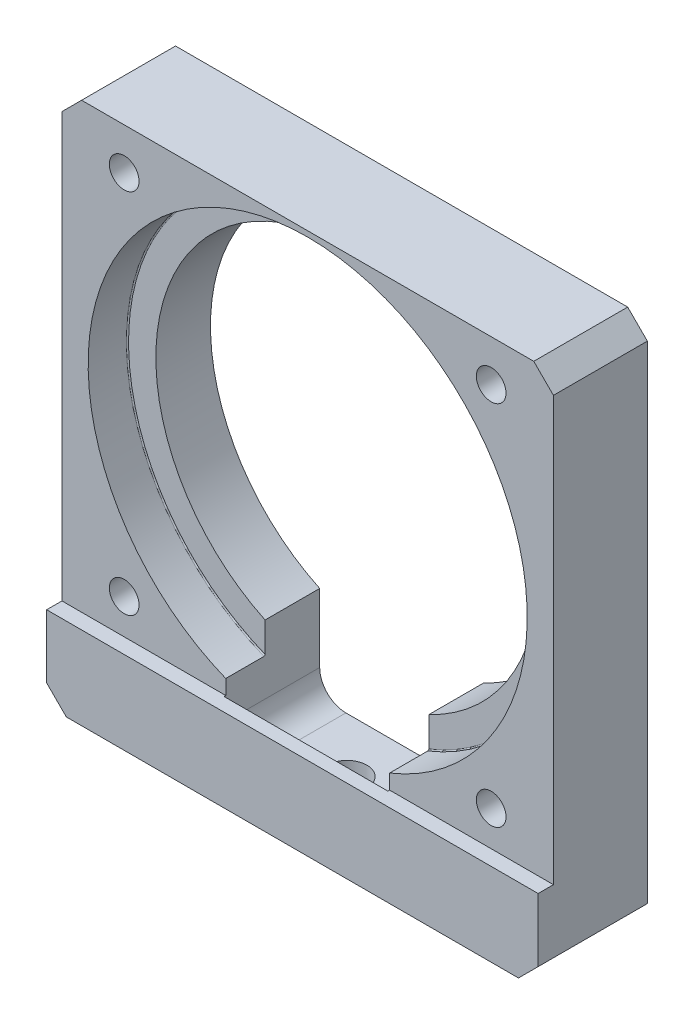
SolidWorks part; units mm, degrees
material "304 SSTL"
ref_plane "Front" through (0, 0, 0) normal (0, 0, 1) x (1, 0, 0)
ref_plane "Top" through (0, 0, 0) normal (0, 1, 0) x (1, 0, 0)
ref_plane "Right" through (0, 0, 0) normal (1, 0, 0) x (0, 0, -1)
sketch "Sketch1" plane through (0, 0, 0) normal (0, 0, 1) x (1, 0, 0)
  line L1 (0, 0) -> (57.15, 0)
  line L2 (0, 0) -> (0, 61.214)
  line L3 (0, 61.214) -> (57.15, 61.214)
  line L4 (57.15, 0) -> (57.15, 61.214)
  dimension "D1" = 57.15
  dimension "D2" = 61.214
extrude "Boss-Extrude1" add sketch "Sketch1" along normal mid plane 12.7
sketch "Sketch2" plane through (0, 0, 6.35) normal (0, 0, 1) x (1, 0, 0)
  line L0 (0, 61.214) -> (0, 0) construction
  line L1 (0, 61.214) -> (57.15, 61.214)
  line L2 (0, 61.214) -> (0, 9.652)
  line L3 (0, 9.652) -> (57.15, 9.652)
  line L4 (57.15, 61.214) -> (57.15, 9.652)
  line L5 (57.15, 0) -> (57.15, 61.214) construction
  line L6 (57.15, 61.214) -> (0, 61.214) construction
  dimension "D1" = 51.562
extrude "Cut-Extrude1" cut sketch "Sketch2" against normal blind 1.778
hole_wizard "1 (1) Diameter Hole1" positions "Sketch4" profile "Sketch5" hole size "1" standard "Ansi Inch" end condition through all
sketch "Sketch4" plane through (0, 0, 4.572) normal (0, 0, 1) x (1, 0, 0)
  line L0 (28.575, 35.052) -> (28.575, 61.214) construction
  line L1 (57.15, 61.214) -> (0, 61.214) construction
  line L2 (0, 9.652) -> (57.15, 9.652) construction
  point P0 (28.575, 35.052)
  dimension "D1" = 25.4
sketch "Sketch5" plane through (28.575, 35.052, 4.572) normal (1, 0, 0) x (0, -1, 0)
  line L0 (0, 0) -> (0, 10.922)
  line L1 (0, 10.922) -> (22.225, 10.922)
  line L2 (22.225, 10.922) -> (22.225, 0)
  line L5 (22.225, 0) -> (0, 0)
  line L11 (0, -6.35) -> (0, 107.95) construction
  dimension "Thru Hole Dia." = 44.45
  dimension "Thru Hole Depth" = 10.922
sketch "Sketch6" plane through (0, 0, -6.35) normal (0, 0, -1) x (-1, 0, 0)
  line L1 (-35.052, 3.9624) -> (-22.098, 3.9624)
  line L2 (-38.1, 7.0104) -> (-38.1, 20.9536)
  line L3 (-38.1, 20.9536) -> (-19.05, 20.9536)
  line L4 (-19.05, 7.0104) -> (-19.05, 20.9536)
  line L5 (-28.575, 3.9624) -> (-28.575, 20.9536) construction
  line L6 (-28.575, 20.9536) -> (-28.575, 61.214) construction
  line L7 (-57.15, 61.214) -> (0, 61.214) construction
  line L8 (0, 0) -> (-57.15, 0) construction
  arc A0 (-22.098, 3.9624) -> (-19.05, 7.0104) centre (-22.098, 7.0104) ccw
  arc A1 (-38.1, 7.0104) -> (-35.052, 3.9624) centre (-35.052, 7.0104) ccw
  point P13 (-19.05, 3.9624)
  point P16 (-38.1, 3.9624)
  dimension "D3" = 3.048
  dimension "D1" = 19.05
  dimension "D2" = 3.9624
extrude "Cut-Extrude2" cut sketch "Sketch6" against normal blind 11.1252
hole_wizard "#14 (0.182) Diameter Hole1" positions "Sketch9" profile "Sketch8" hole size "#14" standard "Ansi Inch"
sketch "Sketch9" plane through (0, 3.9624, 0) normal (0, 1, 0) x (-1, 0, 0)
  line L0 (0, 0) -> (-28.575, 0) construction
  line L1 (-28.575, 0) -> (-28.575, -6.35) construction
  line L2 (0, -6.35) -> (-57.15, -6.35) construction
  point P0 (-28.575, 0)
sketch "Sketch8" plane through (28.575, 3.9624, 0) normal (1, 0, 0) x (0, 0, 1)
  line L0 (0, 0) -> (0, 15.3588)
  line L1 (0, 15.3588) -> (2.3114, 13.97)
  line L2 (2.3114, 13.97) -> (2.3114, 0)
  line L5 (2.3114, 0) -> (0, 0)
  line L10 (0, 15.3588) -> (-2.3114, 13.97) construction
  line L11 (0, -6.35) -> (0, 107.95) construction
  dimension "Hole Dia." = 4.6228
  dimension "Hole Depth" = 13.97
  dimension "Drill Angle" = 118
sketch "Sketch10" plane through (0, 0, 4.572) normal (0, 0, 1) x (1, 0, 0)
  circle A0 centre (28.575, 35.052) radius 25.527
  dimension "D1" = 51.054
extrude "Cut-Extrude3" cut sketch "Sketch10" against normal blind 4.572
chamfer "Chamfer1" distance 2.286 angle 45 4 edges at (57.15, 61.214, -0.889) (57.15, 0, 0) (0, 0, 0) (0, 61.214, -0.889)
hole_wizard "#8-32 Tapped Hole1" positions "Sketch12" profile "Sketch11" tap size "#8-32" standard "Ansi Inch" end condition through all
sketch "Sketch12" plane through (0, 0, 4.572) normal (0, 0, 1) x (1, 0, 0)
  line L0 (7.239, 56.388) -> (49.911, 56.388) construction
  line L1 (7.239, 56.388) -> (7.239, 13.716) construction
  line L2 (7.239, 13.716) -> (49.911, 13.716) construction
  line L3 (49.911, 56.388) -> (49.911, 13.716) construction
  line L4 (28.575, 35.052) -> (28.575, 56.388) construction
  line L5 (28.575, 35.052) -> (49.911, 35.052) construction
  point P0 (7.239, 56.388)
  point P1 (49.911, 56.388)
  point P3 (7.239, 13.716)
  point P5 (49.911, 13.716)
  dimension "D1" = 42.672
sketch "Sketch11" plane through (7.239, 56.388, 4.572) normal (1, 0, 0) x (0, -1, 0)
  line L0 (0, 0) -> (0, 10.922)
  line L1 (0, 10.922) -> (1.7272, 10.922)
  line L2 (1.7272, 10.922) -> (1.7272, 0)
  line L5 (1.7272, 0) -> (0, 0)
  line L11 (0, -6.35) -> (0, 107.95) construction
  dimension "Thru Tap Drill Dia." = 3.4544
  dimension "Thru Tap Drill Depth" = 10.922
cosmetic thread "Hole Thread1" parameters "D2"=4.1656
cosmetic thread "Hole Thread2" parameters "D2"=4.1656
cosmetic thread "Hole Thread3" parameters "D2"=4.1656
cosmetic thread "Hole Thread4" parameters "D2"=4.1656
sketch "Sketch13" plane through (0, 0, 0) normal (0, -1, 0) x (1, 0, 0)
  line L0 (2.286, -6.35) -> (54.864, -6.35) construction
  line L1 (0, -3.175) -> (57.15, -3.175)
  line L2 (0, -3.175) -> (0, -6.35)
  line L3 (0, -6.35) -> (57.15, -6.35)
  line L4 (57.15, -3.175) -> (57.15, -6.35)
  line L5 (0, -6.35) -> (0, 6.35) construction
  line L6 (57.15, 6.35) -> (57.15, -6.35) construction
  dimension "D1" = 3.175
extrude "Cut-Extrude4" cut sketch "Sketch13" against normal blind 2.286
fillet "Fillet1" radius 0.127 1 edges at (28.575, 60.579, 0)
